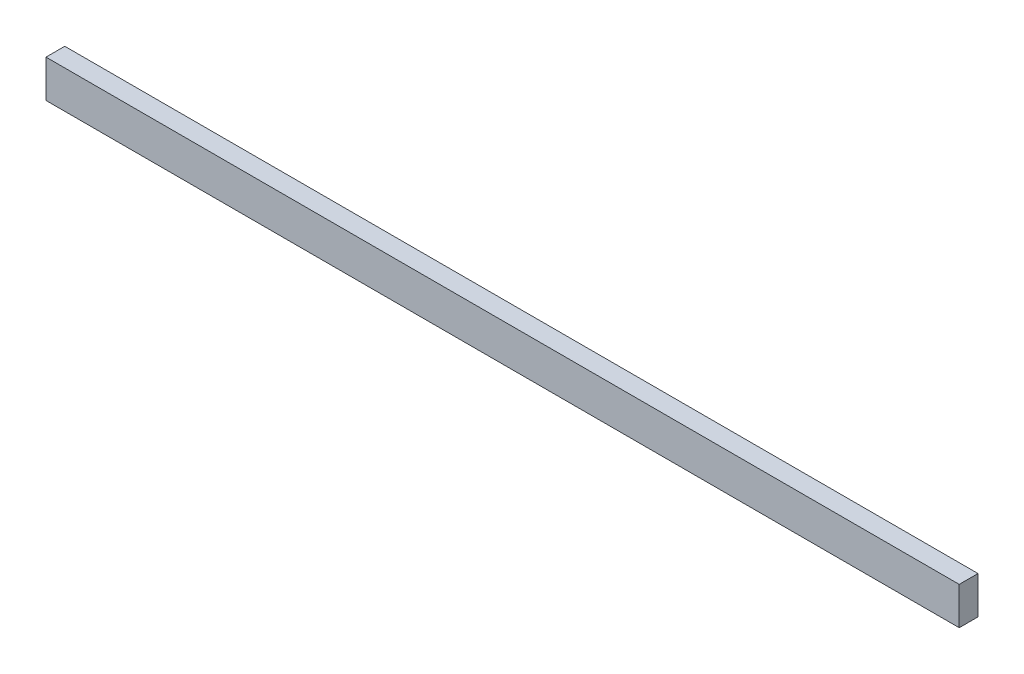
SolidWorks part; units mm, degrees
ref_plane "Front Plane" through (0, 0, 0) normal (0, 0, 1) x (1, 0, 0)
ref_plane "Top Plane" through (0, 0, 0) normal (0, 1, 0) x (1, 0, 0)
ref_plane "Right Plane" through (0, 0, 0) normal (1, 0, 0) x (0, 0, -1)
sketch "Sketch1" plane through (0, 0, 0) normal (0, 1, 0) x (1, 0, 0)
  line L1 (0, 0) -> (1234.9408, 0)
  line L2 (0, 0) -> (0, 25.4)
  line L3 (0, 25.4) -> (1234.9408, 25.4)
  line L4 (1234.9408, 0) -> (1234.9408, 25.4)
  dimension "D1" = 25.4
  dimension "D2" = 1235.202
extrude "Boss-Extrude2" add sketch "Sketch1" along normal blind 50.8 contours L3 L4 L1 L2
